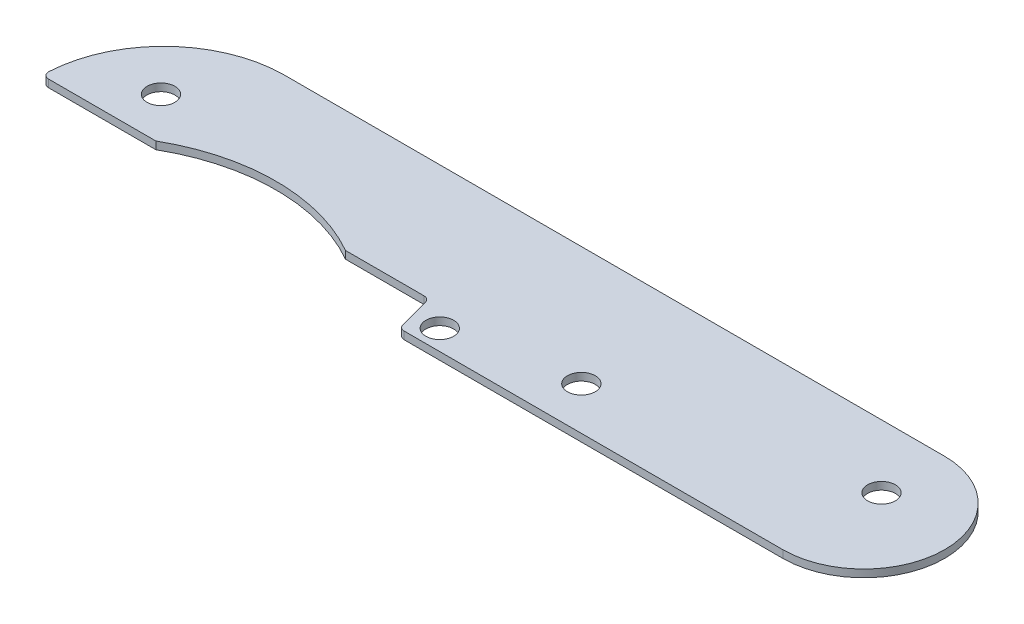
SolidWorks part; units mm, degrees
material "Stainless Steel (ferritic)"
ref_plane "Front Plane" through (0, 0, 0) normal (0, 0, 1) x (1, 0, 0)
ref_plane "Top Plane" through (0, 0, 0) normal (0, 1, 0) x (1, 0, 0)
ref_plane "Right Plane" through (0, 0, 0) normal (1, 0, 0) x (0, 0, -1)
sketch "Sketch1" plane through (0, 0, 0) normal (0, 1, 0) x (1, 0, 0)
  line L0 (0, 8.128) -> (-66.294, 8.128)
  line L1 (-78.486, -4.064) -> (-67.056, -4.064)
  line L2 (-48.006, -4.064) -> (-39.624, -4.064)
  line L3 (-39.624, -4.064) -> (-38.5351, -8.128)
  line L4 (-38.5351, -8.128) -> (0, -8.128)
  line L5 (-78.486, -4.064) -> (-78.486, 4.7664) construction
  arc A0 (0, -8.128) -> (0, 8.128) centre (0, 0) ccw
  arc A1 (-66.294, 8.128) -> (-78.486, -4.064) centre (-66.294, -4.064) ccw
  arc A2 (-67.056, -4.064) -> (-48.006, -4.064) centre (-57.531, -20.6534) cw
  point P1 (8.128, 0)
  point P2 (-78.4804, -3.7009)
  point P14 (-57.531, -1.524)
  point P19 (-78.486, -4.064)
  dimension "D1" = 16.256
  dimension "D2" = 47.752
  dimension "D3" = 12.192
  dimension "D4" = 11.43
  dimension "D5" = 8.382
  dimension "D6" = 86.614
  dimension "D7" = 9.652
  dimension "D8" = 105
extrude "Boss-Extrude1" add sketch "Sketch1" along normal blind 0.762
hole_wizard "3/8 (0.11) Diameter Hole1" positions "Sketch5" profile "Sketch3" hole size "3/8" standard "ANSI Inch" end condition through all
sketch "Sketch5" plane through (0, 0.762, 0) normal (0, 1, 0) x (1, 0, 0)
  line L0 (-78.486, -4.064) -> (-67.056, -4.064) construction
  line L1 (-38.5351, -8.128) -> (0, -8.128) construction
  line L2 (0, 8.128) -> (-66.294, 8.128) construction
  point P0 (-70.866, 0.254)
  point P2 (-36.5031, -6.096)
  point P4 (-24.5651, -3.81)
  point P6 (0, 1.778)
  point P29 (0, 0)
  dimension "D1" = 4.318
  dimension "D2" = 7.62
  dimension "D3" = 2.032
  dimension "D4" = 4.318
  dimension "D5" = 2.032
  dimension "D6" = 13.97
  dimension "D7" = 6.35
sketch "Sketch3" plane through (-70.866, 0.762, -0.254) normal (1, 0, 0) x (0, 0, 1)
  line L0 (0, 0) -> (0, 0.762)
  line L1 (0, 0.762) -> (1.397, 0.762)
  line L2 (1.397, 0.762) -> (1.397, 0)
  line L5 (1.397, 0) -> (0, 0)
  line L11 (0, -6.35) -> (0, 107.95) construction
  dimension "Thru Hole Dia." = 2.794
  dimension "Thru Hole Depth" = 0.762
fillet "Fillet1" radius 0.635 3 edges at (-78.486, 0.381, 4.064) (-38.5351, 0.381, 8.128) (-39.624, 0.381, 4.064)
